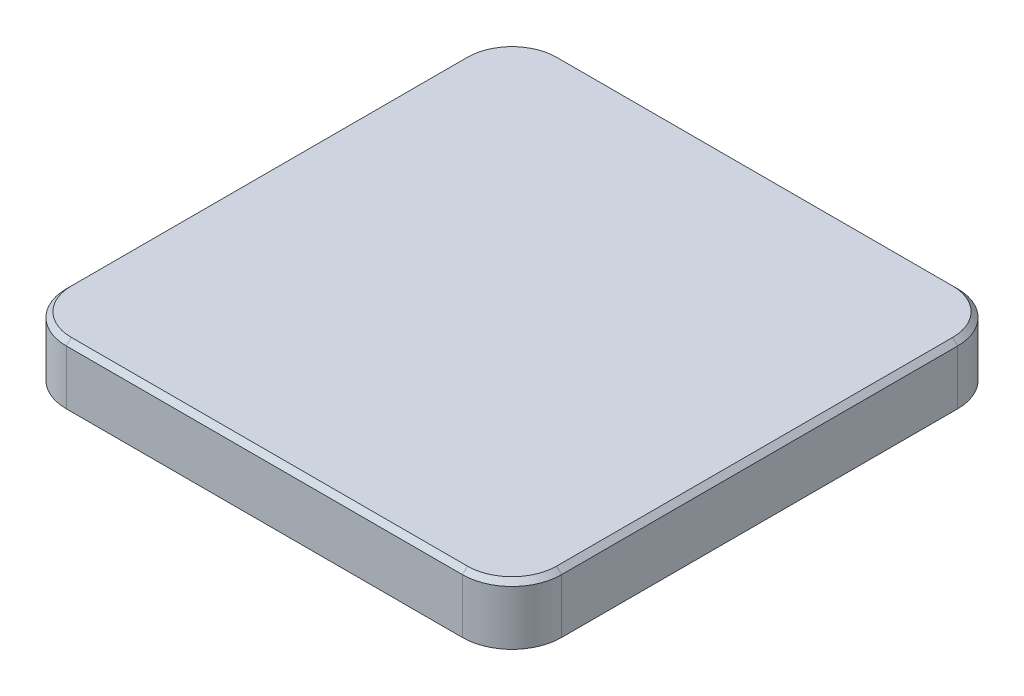
SolidWorks part; units mm, degrees
ref_plane "Alzado" through (0, 0, 0) normal (0, 0, 1) x (1, 0, 0)
ref_plane "Planta" through (0, 0, 0) normal (0, 1, 0) x (1, 0, 0)
ref_plane "Vista lateral" through (0, 0, 0) normal (1, 0, 0) x (0, 0, -1)
sketch "Croquis2" plane through (0, 0, 0) normal (0, 1, 0) x (1, 0, 0)
  line L1 (-40, 50) -> (40, 50)
  line L2 (-50, 40) -> (-50, -40)
  line L3 (-40, -50) -> (40, -50)
  line L4 (50, 40) -> (50, -40)
  line L5 (-50, 50) -> (50, -50) construction
  line L6 (-50, -50) -> (50, 50) construction
  arc A0 (40, 50) -> (50, 40) centre (40, 40) cw
  arc A1 (40, -50) -> (50, -40) centre (40, -40) ccw
  arc A2 (-50, -40) -> (-40, -50) centre (-40, -40) ccw
  arc A3 (-40, 50) -> (-50, 40) centre (-40, 40) ccw
  point P0 (0, 0)
  dimension "D3" = 10
  dimension "D1" = 100
  dimension "D2" = 100
extrude "Saliente-Extruir1" add sketch "Croquis2" along normal blind 12
chamfer "Chaflán1" distance 1 angle 45 8 edges at (47.0711, 12, -47.0711) (0, 12, -50) (-47.0711, 12, -47.0711) (-50, 12, 0) (-47.0711, 12, 47.0711) (0, 12, 50) (47.0711, 12, 47.0711) (50, 12, 0)
